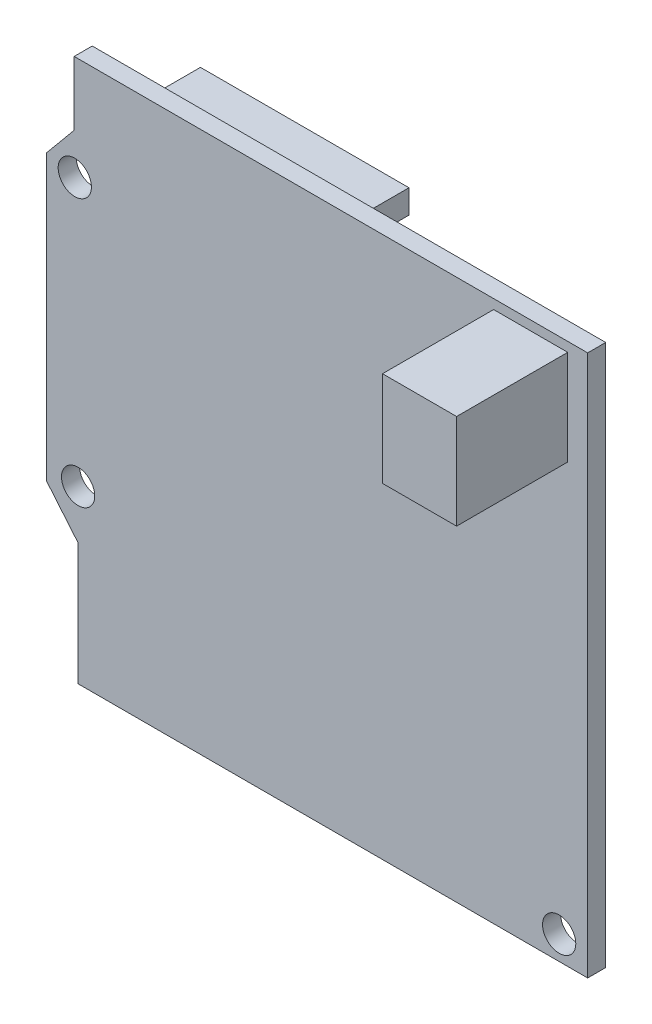
SolidWorks part; units mm, degrees
ref_plane "Ebene vorne" through (0, 0, 0) normal (0, 0, 1) x (1, 0, 0)
ref_plane "Ebene oben" through (0, 0, 0) normal (0, 1, 0) x (1, 0, 0)
ref_plane "Ebene rechts" through (0, 0, 0) normal (1, 0, 0) x (0, 0, -1)
sketch "Sketch1" plane through (0, 0, 0) normal (0, 0, 1) x (1, 0, 0)
  line L1 (28.5, -28.5) -> (-28.5, -28.5)
  line L2 (28.5, -28.5) -> (28.5, 28.5)
  line L3 (28.5, 28.5) -> (-28.5, 28.5)
  line L4 (-28.5, -28.5) -> (-28.5, 28.5)
  line L5 (28.5, -28.5) -> (-28.5, 28.5) construction
  line L6 (28.5, 28.5) -> (-28.5, -28.5) construction
  point P0 (0, 0)
  dimension "D1" = 57
  dimension "D2" = 57
extrude "Boss-Extrude1" add sketch "Sketch1" along normal blind 10.4
sketch "Sketch2" plane through (0, 0, 10.4) normal (0, 0, 1) x (1, 0, 0)
  line L0 (-28.5, 28.5) -> (-28.5, -28.5) construction
  line L1 (26.4, 27.5) -> (18.6, 27.5)
  line L2 (26.4, 27.5) -> (26.4, 17.5)
  line L3 (26.4, 17.5) -> (18.6, 17.5)
  line L4 (18.6, 27.5) -> (18.6, 17.5)
  line L5 (26.4, 27.5) -> (18.6, 17.5) construction
  line L6 (26.4, 17.5) -> (18.6, 27.5) construction
  line L8 (28.5, 28.5) -> (-28.5, 28.5) construction
  point P0 (22.5, 22.5)
  dimension "D1" = 7.8
  dimension "D2" = 10
  dimension "D3" = 51
  dimension "D4" = 6
extrude "Boss-Extrude3" add sketch "Sketch2" along normal blind 11.7
hole_wizard "Ø3.5 (3.5) Diameter Hole1" positions "Sketch5" profile "Sketch4" hole size "Ø3.5" standard "DIN" end condition up to next
sketch "Sketch5" plane through (0, 0, 10.4) normal (0, 0, 1) x (1, 0, 0)
  line L0 (28.5, 28.5) -> (-28.5, 28.5) construction
  line L1 (-28.5, 28.5) -> (-28.5, -28.5) construction
  line L2 (-28.5, -28.5) -> (28.5, -28.5) construction
  line L3 (28.5, -28.5) -> (28.5, 28.5) construction
  point P0 (-25.5, 17.5)
  point P2 (-25.1486, -10.5)
  point P4 (25.5, -26)
  dimension "D1" = 11
  dimension "D2" = 3
  dimension "D3" = 28
  dimension "D4" = 2.5
  dimension "D5" = 3
sketch "Sketch4" plane through (-25.5, 17.5, 10.4) normal (1, 0, 0) x (0, -1, 0)
  line L0 (0, 0) -> (0, 10.4)
  line L1 (0, 10.4) -> (1.75, 10.4)
  line L2 (1.75, 10.4) -> (1.75, 0)
  line L5 (1.75, 0) -> (0, 0)
  line L11 (0, -6.35) -> (0, 107.95) construction
  dimension "Thru Hole Dia." = 3.5
  dimension "Thru Hole Depth" = 10.4
sketch "Sketch6" plane through (0, 0, 10.4) normal (0, 0, 1) x (1, 0, 0)
  line L0 (-25.5624, 28.5) -> (-25.5624, 21.7695)
  line L1 (28.5, 28.5) -> (-28.5, 28.5) construction
  line L2 (-25.5624, 21.7695) -> (-28.5, 18.2226)
  line L3 (-28.5, 28.5) -> (-28.5, -28.5) construction
  line L4 (-28.5, 18.2226) -> (-28.5, 28.5)
  line L5 (-28.5, 28.5) -> (-25.5624, 28.5)
  line L6 (-25.1693, -15.6221) -> (-28.5, -11.6385)
  line L7 (-28.5, -11.6385) -> (-28.5, -28.5)
  line L8 (-28.5, -28.5) -> (-25.1693, -28.5)
  line L9 (-28.5, -28.5) -> (28.5, -28.5) construction
  line L10 (-25.1693, -28.5) -> (-25.1693, -15.6221)
extrude "Cut-Extrude1" cut sketch "Sketch6" against normal up to next
sketch "Sketch7" plane through (0, 0, 0) normal (0, 0, -1) x (-1, 0, 0)
  line L0 (25.1693, -28.5) -> (-28.5, -28.5) construction
  line L1 (0.7131, 23.75) -> (22.6693, 23.75)
  line L2 (0.7131, 23.75) -> (0.7131, 21.25)
  line L3 (0.7131, 21.25) -> (22.6693, 21.25)
  line L4 (22.6693, 23.75) -> (22.6693, 21.25)
  line L5 (-19.3307, -25) -> (22.6693, -25)
  line L6 (-19.3307, -25) -> (-19.3307, -27.5)
  line L7 (-19.3307, -27.5) -> (22.6693, -27.5)
  line L8 (22.6693, -25) -> (22.6693, -27.5)
  line L9 (25.1693, -15.6221) -> (25.1693, -28.5) construction
  line L18 (-28.5, -28.5) -> (25.1693, -28.5)
  line L19 (25.1693, -28.5) -> (25.1693, -15.6221)
  line L20 (25.1693, -15.6221) -> (28.5, -11.6385)
  line L21 (28.5, -11.6385) -> (28.5, 18.2226)
  line L22 (28.5, 18.2226) -> (25.5624, 21.7695)
  line L23 (25.5624, 21.7695) -> (25.5624, 28.5)
  line L24 (25.5624, 28.5) -> (-28.5, 28.5)
  line L25 (-28.5, 28.5) -> (-28.5, -28.5)
  line L26 (-28.5, -28.5) -> (25.1693, -28.5)
  line L27 (25.1693, -28.5) -> (25.1693, -15.6221)
  line L28 (25.1693, -15.6221) -> (28.5, -11.6385)
  line L29 (28.5, -11.6385) -> (28.5, 18.2226)
  line L30 (28.5, 18.2226) -> (25.5624, 21.7695)
  line L31 (25.5624, 21.7695) -> (25.5624, 28.5)
  line L32 (25.5624, 28.5) -> (-28.5, 28.5)
  line L33 (-28.5, 28.5) -> (-28.5, -28.5)
  dimension "D1" = 1
  dimension "D2" = 42
  dimension "D3" = 2.5
  dimension "D4" = 2.5
  dimension "D5" = 46.25
  dimension "D6" = 2.5
  dimension "D7" = 21.9562
  dimension "D8" = 0
extrude "Cut-Extrude2" cut sketch "Sketch7" against normal blind 8.5
